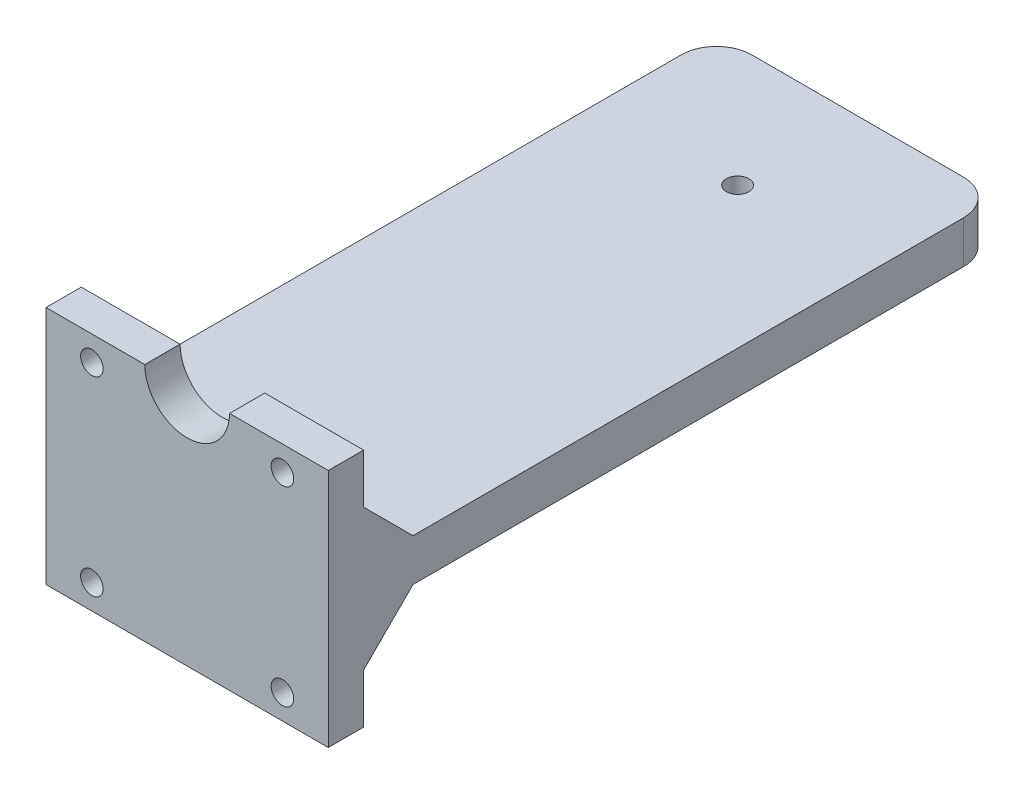
SolidWorks part; units mm, degrees
material "PET"
ref_plane "Спереди" through (0, 0, 0) normal (0, 0, 1) x (1, 0, 0)
ref_plane "Сверху" through (0, 0, 0) normal (0, 1, 0) x (1, 0, 0)
ref_plane "Справа" through (0, 0, 0) normal (1, 0, 0) x (0, 0, -1)
sketch "Эскиз1" plane through (0, 0, 0) normal (0, 1, 0) x (1, 0, 0)
  line L1 (20, 95) -> (-20, 95)
  line L2 (20, 95) -> (20, 0)
  line L3 (20, 0) -> (-20, 0)
  line L4 (-20, 95) -> (-20, 0)
  line L5 (20, 95) -> (-20, 0) construction
  line L6 (20, 0) -> (-20, 95) construction
  point P0 (0, 47.5)
  dimension "D1" = 40
  dimension "D2" = 95
extrude "Бобышка-Вытянуть1" add sketch "Эскиз1" along normal blind 6
sketch "Эскиз2" plane through (0, 6, 0) normal (0, 1, 0) x (1, 0, 0)
  line L0 (20, 0) -> (20, 95) construction
  line L1 (-20, 0) -> (20, 0)
  line L2 (-20, 0) -> (-20, 5)
  line L3 (-20, 5) -> (20, 5)
  line L4 (20, 0) -> (20, 5)
  dimension "D1" = 5
extrude "Бобышка-Вытянуть2" add sketch "Эскиз2" along normal blind 14
sketch "Эскиз3" plane through (0, 0, -5) normal (0, 0, -1) x (-1, 0, 0)
  line L0 (-20, 20) -> (20, 20) construction
  circle A0 centre (0, 20) radius 6
  dimension "D1" = 12
extrude "Вырез-Вытянуть1" cut sketch "Эскиз3" against normal blind 14
sketch "Эскиз4" plane through (0, 0, -5) normal (0, 0, -1) x (-1, 0, 0)
  line L0 (0, 20) -> (0, -2.6292) construction
  line L1 (-20, 20) -> (-6, 20) construction
  circle A0 centre (-13.5, 16.5) radius 1.6
  circle A1 centre (13.5, 16.5) radius 1.6
  dimension "D1" = 3.2
  dimension "D2" = 3.5
  dimension "D3" = 27
extrude "Вырез-Вытянуть2" cut sketch "Эскиз4" against normal blind 14
chamfer "Фаска1" distance 7 angle 45 1 edges at (0, 6, -5)
sketch "Эскиз5" plane through (0, 0, 0) normal (0, -1, 0) x (1, 0, 0)
  circle A0 centre (0, -78) radius 7
  dimension "D2" = 14
  dimension "D1" = 78
fillet "Скругление1" radius 5 2 edges at (-20, 3, -95) (20, 3, -95)
sketch "Эскиз7" plane through (-20, 0, 0) normal (-1, 0, 0) x (0, 0, 1)
  line L0 (-90, 3) -> (0, 3) construction
  line L1 (0, -14) -> (-5, -14)
  line L2 (-5, -14) -> (-5, -7)
  line L3 (-5, -7) -> (-12, 0)
  line L4 (-12, 0) -> (0, 0)
  line L7 (-12, 6) -> (-90, 6)
  line L8 (-90, 6) -> (-90, 0)
  line L9 (-90, 0) -> (0, 0)
  line L10 (0, 0) -> (0, 20)
  line L11 (0, 20) -> (-5, 20)
  line L12 (-5, 20) -> (-5, 13)
  line L13 (-5, 13) -> (-12, 6)
  line L17 (0, -14) -> (0, 0)
  point P11 (0, 3)
  dimension "D1" = 0
extrude "Бобышка-Вытянуть3" add sketch "Эскиз7" against normal blind 40
sketch "Эскиз8" plane through (0, 0, 0) normal (0, 0, 1) x (1, 0, 0)
  line L0 (-20, 3) -> (20, 3) construction
  line L1 (-20, 20) -> (-20, -14) construction
  line L2 (20, 20) -> (20, -14) construction
  circle A0 centre (13.5, 16.5) radius 1.6 construction
  circle A1 centre (-13.5, 16.5) radius 1.6 construction
  circle A2 centre (13.5, 16.5) radius 1.6
  circle A3 centre (-13.5, 16.5) radius 1.6
  circle A4 centre (13.5, -10.5) radius 1.6
  circle A5 centre (-13.5, -10.5) radius 1.6
extrude "Вырез-Вытянуть3" cut sketch "Эскиз8" against normal blind 40
extrude "Бобышка-Вытянуть4" add sketch "Эскиз5" along normal blind 2
sketch "Эскиз9" plane through (0, -2, 0) normal (0, -1, 0) x (1, 0, 0)
  circle A0 centre (0, -78) radius 6.05
  dimension "D1" = 12.1
extrude "Бобышка-Вытянуть5" add sketch "Эскиз9" along normal blind 4
chamfer "Фаска2" distance 0.5 angle 45 1 edges at (0, -6, -84.05)
sketch "Эскиз10" plane through (0, -6, 0) normal (0, -1, 0) x (1, 0, 0)
  circle A0 centre (0, -78) radius 1.6
  dimension "D1" = 3.2
extrude "Вырез-Вытянуть4" cut sketch "Эскиз10" against normal through all
